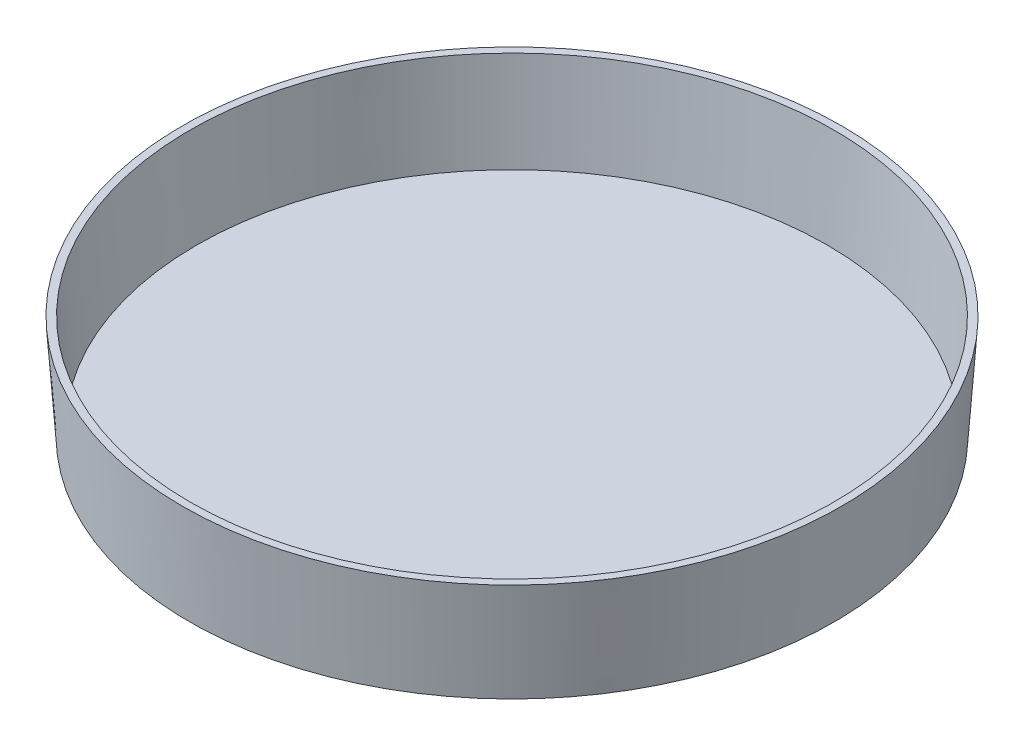
SolidWorks part; units mm, degrees
ref_plane "Front Plane" through (0, 0, 0) normal (0, 0, 1) x (1, 0, 0)
ref_plane "Top Plane" through (0, 0, 0) normal (0, 1, 0) x (1, 0, 0)
ref_plane "Right Plane" through (0, 0, 0) normal (1, 0, 0) x (0, 0, -1)
sketch "Sketch2" plane through (0, 0, 0) normal (0, 0, 1) x (1, 0, 0)
  line L0 (0, 0) -> (43.8785, 0)
  line L1 (0, 14.1224) -> (44.8564, 14.1224)
  line L2 (44.8564, 14.1224) -> (43.8785, 0)
  line L3 (0, 0) -> (0, 14.1224) construction
  line L4 (0, 0) -> (0, 14.1224)
  dimension "D1" = 43.8785
  dimension "D2" = 14.1224
  dimension "D3" = 44.8564
revolve "Revolve1" add sketch "Sketch2" angle 360 about L3
shell "Shell1" thickness 1.016
sketch "Sketch3" plane through (0, 0, 0) normal (0, -1, 0) x (1, 0, 0)
  circle A1 centre (0, 0) radius 40.1447
  circle A2 centre (0, 0) radius 40.8305
  circle A3 centre (0, 0) radius 40.8305
  dimension "D1" = 3.048
  dimension "D2" = 0.6858
extrude "Boss-Extrude1" add sketch "Sketch3" along normal blind 0.762
